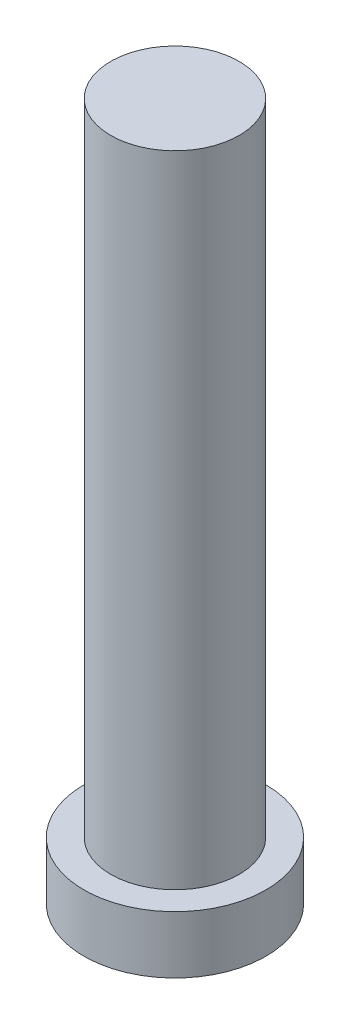
SolidWorks part; units mm, degrees
ref_plane "Front Plane" through (0, 0, 0) normal (0, 0, 1) x (1, 0, 0)
ref_plane "Top Plane" through (0, 0, 0) normal (0, 1, 0) x (1, 0, 0)
ref_plane "Right Plane" through (0, 0, 0) normal (1, 0, 0) x (0, 0, -1)
sketch "Sketch1" plane through (0, 0, 0) normal (0, 1, 0) x (1, 0, 0)
  circle A0 centre (0, 0) radius 3.35
  dimension "D1" = 6.7
extrude "Boss-Extrude1" add sketch "Sketch1" along normal blind 33.4
sketch "Sketch2" plane through (0, 0, 0) normal (0, -1, 0) x (1, 0, 0)
  circle A0 centre (0, 0) radius 4.75
  dimension "D1" = 9.5
extrude "Boss-Extrude2" add sketch "Sketch2" along normal blind 3
